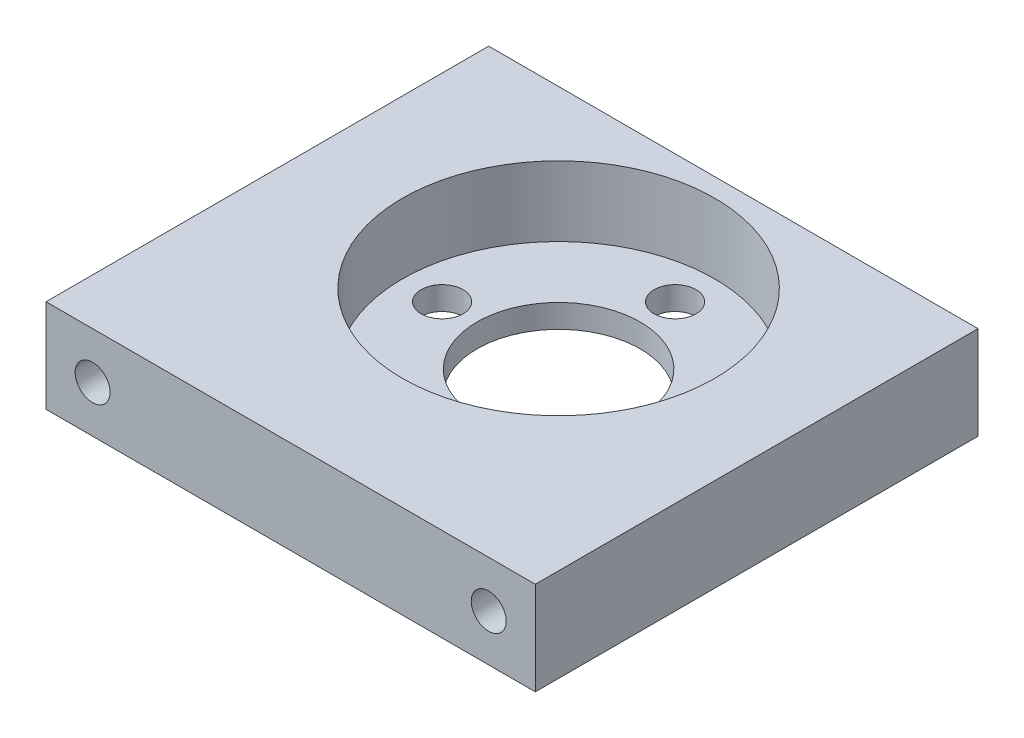
SolidWorks part; units mm, degrees
material "Alliage 1060"
ref_plane "Plan de face" through (0, 0, 0) normal (0, 0, 1) x (1, 0, 0)
ref_plane "Plan de dessus" through (0, 0, 0) normal (0, 1, 0) x (1, 0, 0)
ref_plane "Plan de droite" through (0, 0, 0) normal (1, 0, 0) x (0, 0, -1)
sketch "Esquisse1" plane through (0, 0, 0) normal (0, 1, 0) x (1, 0, 0)
  line L1 (0, 0) -> (42, 0)
  line L2 (0, 0) -> (0, 46)
  line L3 (0, 46) -> (42, 46)
  line L4 (42, 0) -> (42, 46)
  dimension "D1" = 42
  dimension "D2" = 46
extrude "Boss.-Extru.1" add sketch "Esquisse1" along normal blind 8
sketch "Esquisse2" plane through (0, 8, 0) normal (0, 1, 0) x (1, 0, 0)
  line L2 (0, 23) -> (42, 23) construction
  line L3 (0, 46) -> (0, 0) construction
  line L4 (42, 0) -> (42, 46) construction
  circle A0 centre (21, 23) radius 13.4
  point P9 (21, 23)
  dimension "D1" = 26.8
extrude "Enlèv. mat.-Extru.1" cut sketch "Esquisse2" against normal blind 6
sketch "Esquisse3" plane through (0, 2, 0) normal (0, 1, 0) x (1, 0, 0)
  line L0 (21, 23) -> (21, 33) construction
  circle A0 centre (21, 23) radius 7
  circle A1 centre (21, 33) radius 1.8
  circle A2 centre (31, 23) radius 1.8
  circle A3 centre (21, 13) radius 1.8
  circle A4 centre (11, 23) radius 1.8
  point P14 (21, 23)
  dimension "D1" = 14
  dimension "D3" = 3.6
  dimension "D2" = 10
  dimension "D4" = 4
extrude "Enlèv. mat.-Extru.2" cut sketch "Esquisse3" against normal through all
sketch "Esquisse4" plane through (0, 0, -46) normal (0, 0, -1) x (-1, 0, 0)
  line L0 (-42, 4) -> (0, 4) construction
  line L1 (-42, 8) -> (-42, 0) construction
  line L2 (0, 8) -> (0, 0) construction
  circle A0 centre (-38, 4) radius 1.5
  circle A1 centre (-4, 4) radius 1.5
  dimension "D1" = 3
  dimension "D2" = 4
  dimension "D3" = 4
extrude "Enlèv. mat.-Extru.3" cut sketch "Esquisse4" against normal through all
sketch "Esquisse5" plane through (0, 8, 0) normal (0, 1, 0) x (1, 0, 0)
  line L0 (42, 0) -> (42, 46) construction
  line L1 (0, 46) -> (42, 46)
  line L2 (0, 46) -> (0, 38)
  line L3 (0, 38) -> (42, 38)
  line L4 (42, 46) -> (42, 38)
  dimension "D1" = 8
extrude "Enlèv. mat.-Extru.4" cut sketch "Esquisse5" against normal up to next
